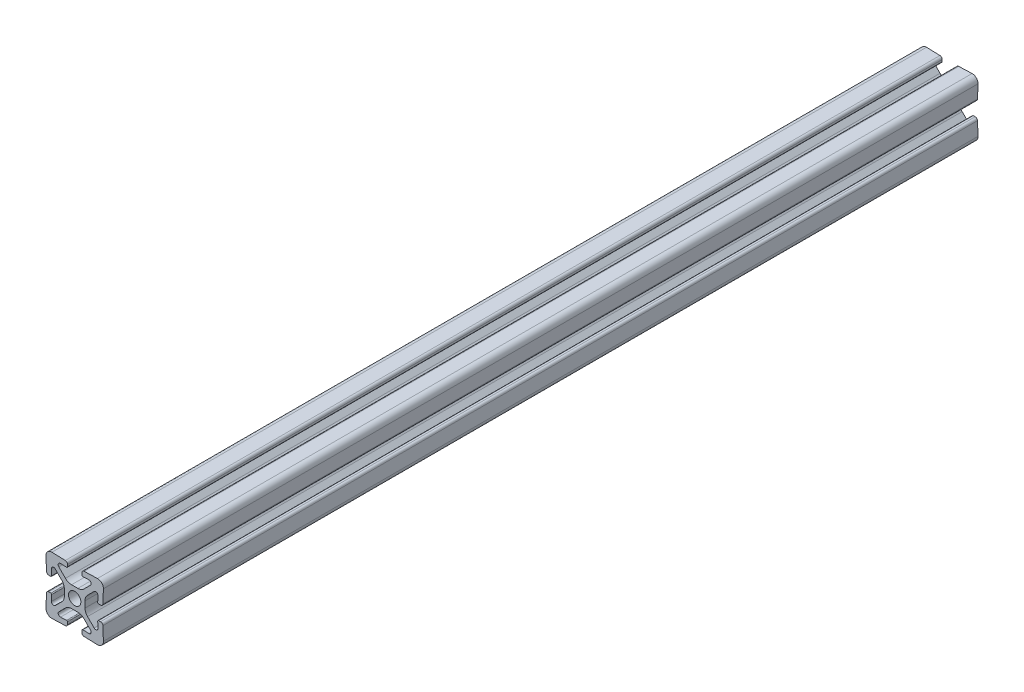
SolidWorks part; units mm, degrees
ref_plane "Front Plane" through (0, 0, 0) normal (0, 0, 1) x (1, 0, 0)
ref_plane "Top Plane" through (0, 0, 0) normal (0, 1, 0) x (1, 0, 0)
ref_plane "Right Plane" through (0, 0, 0) normal (1, 0, 0) x (0, 0, -1)
sketch "Sketch1" plane through (0, 0, 0) normal (0, 0, 1) x (1, 0, 0)
  line L0 (0, 0) -> (0, 10) construction
  line L1 (0, 0) -> (10, 0) construction
  line L2 (0, 0) -> (-10, 10) construction
  line L3 (-7.9302, 9.9988) -> (-3.2721, 9.8361)
  line L4 (-10, 10) -> (0, 10) construction
  line L6 (-2.8352, 8.0198) -> (-4.953, 8.0937)
  line L10 (0, 3.6) -> (-1.1022, 3.6)
  line L11 (-3.2236, 4.4787) -> (-5.5244, 6.7796)
  line L24 (0, 0) -> (-10, 0) construction
  line L25 (-10, 0) -> (0, 0) construction
  line L26 (0, 0) -> (0, -10) construction
  line L27 (-10, -10) -> (-10, 10) construction
  line L28 (0, 10) -> (10, 10) construction
  line L29 (-2.5249, 8.3091) -> (-2.5005, 9.0087)
  line L30 (-10, -10) -> (10, -10) construction
  arc A0 (-9.4142, 9.4142) -> (-7.9302, 9.9988) centre (-8, 8) cw
  arc A5 (-3.2721, 9.8361) -> (-2.5005, 9.0087) centre (-3.3, 9.0366) cw
  arc A6 (-1.1022, 3.6) -> (-3.2236, 4.4787) centre (-1.1022, 6.6) cw
  circle A16 centre (0, 0) radius 2.15
  arc A18 (-5.5244, 6.7796) -> (-4.953, 8.0937) centre (-4.9799, 7.3241) cw
  arc A20 (-2.8352, 8.0198) -> (-2.5249, 8.3091) centre (-2.8247, 8.3196) ccw
  point P15 (0, 0)
  point P42 (-2.3449, 3.6)
  point P80 (-10, 0)
  point P85 (0, -10)
  point P88 (0, -10)
  dimension "D11" = 2
  dimension "D15" = 3
  dimension "Center Hole Diameter" = 4.3
  dimension "D7" = 0.8
  dimension "D8" = 0.3
  dimension "D4" = 0.7701
  dimension "D1" = 45
  dimension "D2" = 2
  dimension "Rail Width" = 20
  dimension "T-Slot Depth" = 6.4
  dimension "D9" = 1.8
  dimension "Rail Height" = 20
  dimension "D23" = 7.2
  dimension "D5" = 11.5
  dimension "T-Slot Width" = 5
  dimension "D3" = 1.775
  dimension "D6" = 9.9598
sketch "Sketch2" plane through (0, 0, 0) normal (1, 0, 0) x (0, 0, -1)
  line L0 (-152.4, 0) -> (152.4, 0)
  line L1 (-152.4, -10) -> (-152.4, 10)
  line L2 (0, 0) -> (0, 10) construction
  line L3 (0, 0) -> (0, 10) construction
  line L4 (152.4, -10) -> (152.4, 10)
  point P0 (-122.4, 0)
  point P3 (0, 0)
  point P7 (122.4, 0)
  point P11 (-152.4, 0)
  point P14 (152.4, 0)
  dimension "D1" = 30
  dimension "Length" = 304.8
sketch "Sketch3" plane through (0, 0, 0) normal (0, 0, 1) x (1, 0, 0)
  line L0 (-2.5249, 8.3091) -> (-2.5005, 9.0087) construction
  line L1 (0, 0) -> (-10, 10) construction
  line L2 (0, 0) -> (-10, 10) construction
  line L5 (-7.9302, 9.9988) -> (-3.2721, 9.8361) construction
  line L6 (-2.8352, 8.0198) -> (-4.953, 8.0937) construction
  line L17 (-2.5249, 8.3091) -> (-2.5005, 9.0087)
  line L19 (-2.8352, 8.0198) -> (-4.953, 8.0937)
  line L20 (0, 0) -> (0, 10) construction
  line L21 (-3.6, 0) -> (-2.15, 0)
  line L22 (-3.6, 0) -> (-3.6, 1.1022)
  line L23 (-4.4787, 3.2236) -> (-6.7796, 5.5244)
  line L42 (-3.2236, 4.4787) -> (-5.5244, 6.7796) construction
  line L43 (0, 3.6) -> (-1.1022, 3.6) construction
  line L44 (-7.9302, 9.9988) -> (-3.2721, 9.8361)
  line L47 (-3.2236, 4.4787) -> (-5.5244, 6.7796)
  line L48 (0, 3.6) -> (-1.1022, 3.6)
  line L59 (0, 3.6) -> (0, 2.15)
  line L60 (-9.9988, 7.9302) -> (-9.8361, 3.2721)
  line L61 (-8.0198, 2.8352) -> (-8.0937, 4.953)
  line L62 (-8.3091, 2.5249) -> (-9.0087, 2.5005)
  arc A0 (-7.9302, 9.9988) -> (-9.4142, 9.4142) centre (-8, 8) ccw construction
  arc A1 (-2.8352, 8.0198) -> (-2.5249, 8.3091) centre (-2.8247, 8.3196) ccw construction
  arc A3 (-2.8352, 8.0198) -> (-2.5249, 8.3091) centre (-2.8247, 8.3196) ccw
  arc A5 (-7.9302, 9.9988) -> (-9.9988, 7.9302) centre (-8, 8) ccw
  circle A13 centre (0, 0) radius 2.15 construction
  arc A14 (0, 2.15) -> (-2.15, 0) centre (0, 0) ccw
  arc A15 (-4.4787, 3.2236) -> (-3.6, 1.1022) centre (-6.6, 1.1022) cw
  arc A16 (-8.0937, 4.953) -> (-6.7796, 5.5244) centre (-7.3241, 4.9799) cw
  arc A17 (-9.0087, 2.5005) -> (-9.8361, 3.2721) centre (-9.0366, 3.3) cw
  arc A18 (-8.0198, 2.8352) -> (-8.3091, 2.5249) centre (-8.3196, 2.8247) cw
  arc A36 (-2.5005, 9.0087) -> (-3.2721, 9.8361) centre (-3.3, 9.0366) ccw construction
  arc A38 (-4.953, 8.0937) -> (-5.5244, 6.7796) centre (-4.9799, 7.3241) ccw construction
  arc A39 (-3.2236, 4.4787) -> (-1.1022, 3.6) centre (-1.1022, 6.6) ccw construction
  arc A41 (-2.5005, 9.0087) -> (-3.2721, 9.8361) centre (-3.3, 9.0366) ccw
  arc A43 (-4.953, 8.0937) -> (-5.5244, 6.7796) centre (-4.9799, 7.3241) ccw
  arc A44 (-3.2236, 4.4787) -> (-1.1022, 3.6) centre (-1.1022, 6.6) ccw
extrude "Boss-Extrude1" add sketch "Sketch3" along normal mid plane 304.8
pattern_circular "CirPattern1" count 4 over 360 about axis through (0, 0, 0) along (0, 0, 1) of "Boss-Extrude1"
ref_plane "Contact Plane 1" through (0, 10, 0) normal (0, 1, 0) x (1, 0, 0)
ref_plane "Contact Plane 2" through (10, 0, 0) normal (1, 0, 0) x (0, 0, -1)
ref_plane "Contact Plane 3" through (0, -10, 0) normal (0, -1, 0) x (-1, 0, 0)
ref_plane "Contact Plane 4" through (-10, 0, 0) normal (-1, 0, 0) x (0, 0, 1)
equation "\"D1@Sketch2\"=\"Rail Width@Sketch1\"*1.5"
equation "\"D1@Boss-Extrude1\" = \"Length@Sketch2\""
